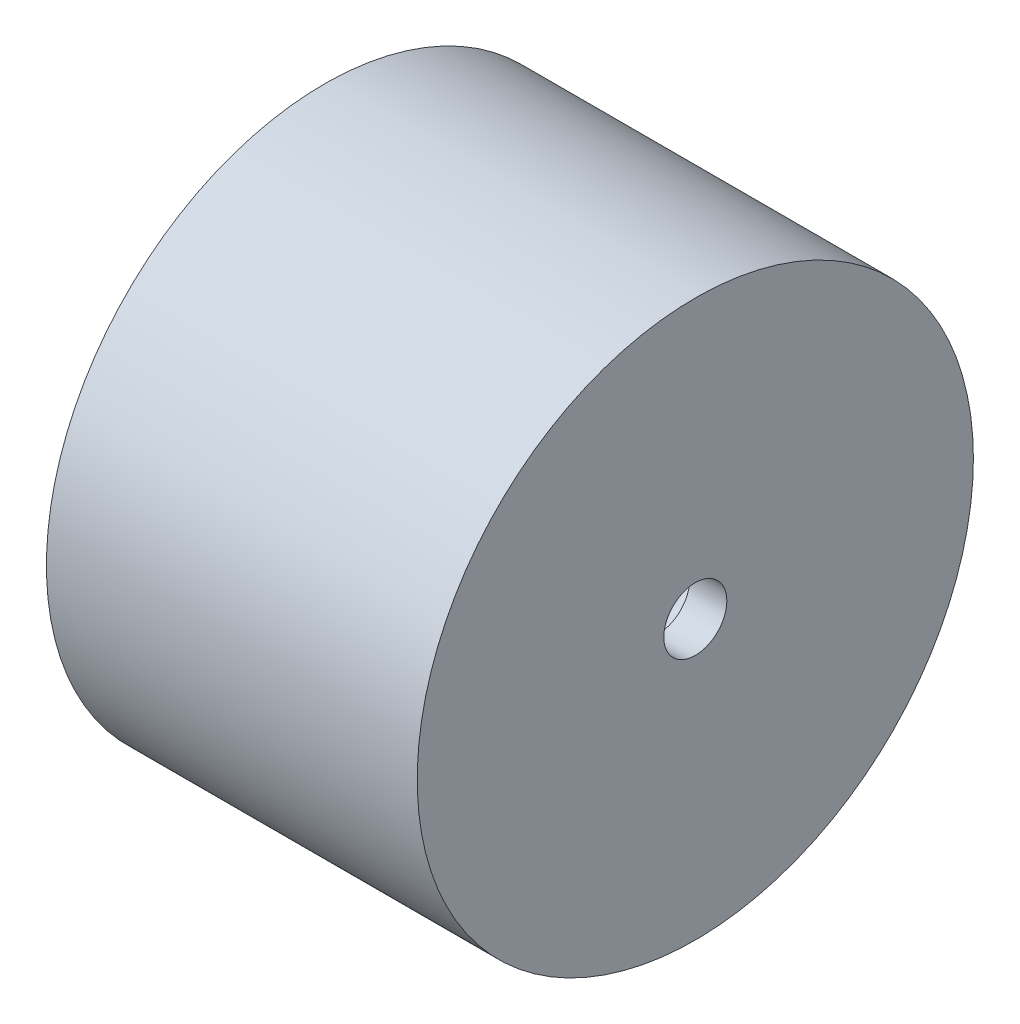
SolidWorks part; units mm, degrees
ref_plane "Front Plane" through (0, 0, 0) normal (0, 0, 1) x (1, 0, 0)
ref_plane "Top Plane" through (0, 0, 0) normal (0, 1, 0) x (1, 0, 0)
ref_plane "Right Plane" through (0, 0, 0) normal (1, 0, 0) x (0, 0, -1)
sketch "Sketch1" plane through (0, 0, 0) normal (1, 0, 0) x (0, 0, -1)
  circle A0 centre (0, 0) radius 15
extrude "Boss-Extrude3" add sketch "Sketch1" along normal blind 20
shell "Shell2" thickness 2
sketch "Sketch2" plane through (20, 0, 0) normal (1, 0, 0) x (0, 0, -1)
  circle A0 centre (0, 0) radius 1.7
extrude "Cut-Extrude1" cut sketch "Sketch2" against normal blind 2
